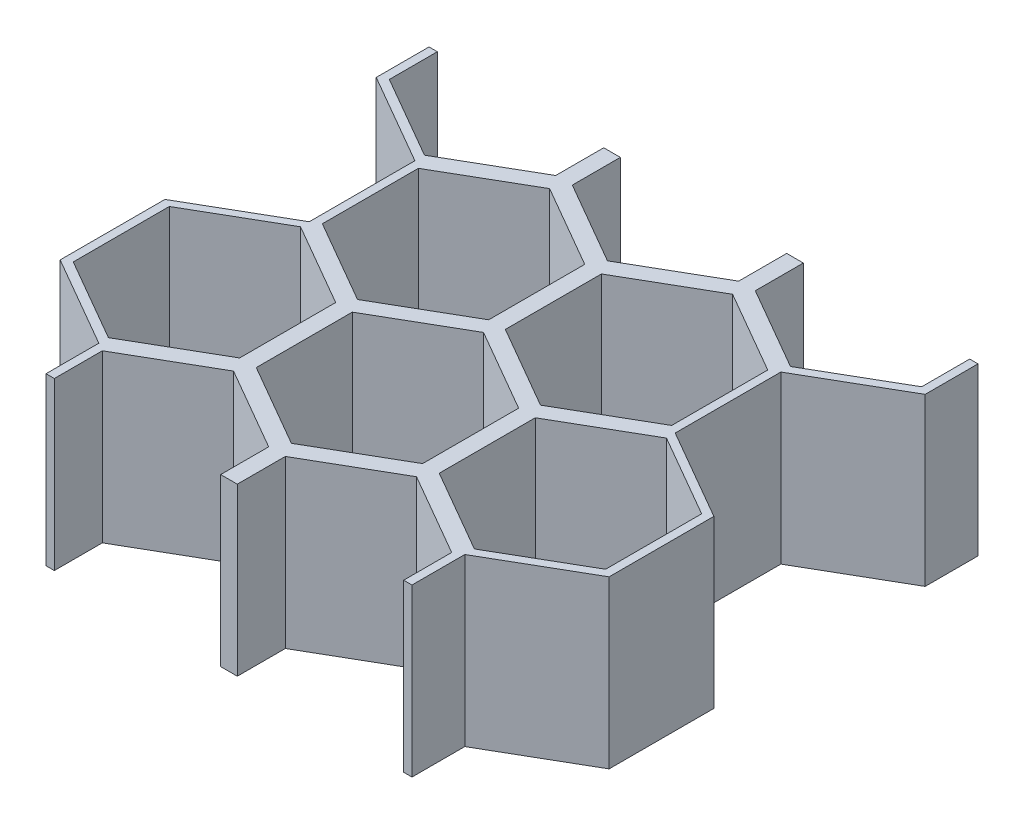
SolidWorks part; units mm, degrees
ref_plane "Front Plane" through (0, 0, 0) normal (0, 0, 1) x (1, 0, 0)
ref_plane "Top Plane" through (0, 0, 0) normal (0, 1, 0) x (1, 0, 0)
ref_plane "Right Plane" through (0, 0, 0) normal (1, 0, 0) x (0, 0, -1)
sketch "Sketch1" plane through (0, 0, 0) normal (0, 1, 0) x (1, 0, 0)
  line L0 (22, 11.547) -> (12, 5.7735)
  line L1 (0, 11.547) -> (-10, 5.7735)
  line L2 (-10, 5.7735) -> (-10, -5.7735)
  line L3 (-10, -5.7735) -> (0, -11.547)
  line L4 (0, -11.547) -> (10, -5.7735)
  line L5 (10, -5.7735) -> (10, 5.7735)
  line L6 (10, 5.7735) -> (0, 11.547)
  line L7 (11, -30.5996) -> (21, -24.8261)
  line L8 (21, -24.8261) -> (21, -13.2791)
  line L9 (21, -13.2791) -> (11, -7.5056)
  line L10 (11, -7.5056) -> (1, -13.2791)
  line L11 (1, -13.2791) -> (1, -24.8261)
  line L12 (1, -24.8261) -> (11, -30.5996)
  line L13 (12, 5.7735) -> (12, -5.7735)
  line L14 (12, -5.7735) -> (22, -11.547)
  line L15 (22, -11.547) -> (32, -5.7735)
  line L16 (32, -5.7735) -> (32, 5.7735)
  line L17 (32, 5.7735) -> (22, 11.547)
  line L18 (33, -30.5996) -> (43, -24.8261)
  line L19 (43, -24.8261) -> (43, -13.2791)
  line L20 (43, -13.2791) -> (33, -7.5056)
  line L21 (33, -7.5056) -> (23, -13.2791)
  line L22 (23, -13.2791) -> (23, -24.8261)
  line L23 (23, -24.8261) -> (33, -30.5996)
  line L24 (44, 11.547) -> (34, 5.7735)
  line L25 (34, 5.7735) -> (34, -5.7735)
  line L26 (34, -5.7735) -> (44, -11.547)
  line L27 (44, -11.547) -> (54, -5.7735)
  line L28 (54, -5.7735) -> (54, 5.7735)
  line L29 (54, 5.7735) -> (44, 11.547)
  line L30 (55, -30.5996) -> (65, -24.8261)
  line L31 (65, -24.8261) -> (65, -13.2791)
  line L32 (65, -13.2791) -> (55, -7.5056)
  line L33 (55, -7.5056) -> (45, -13.2791)
  line L34 (45, -13.2791) -> (45, -24.8261)
  line L35 (45, -24.8261) -> (55, -30.5996)
  line L36 (22, 49.547) -> (12, 43.7735)
  line L37 (12, 43.7735) -> (12, 32.2265)
  line L38 (12, 32.2265) -> (22, 26.453)
  line L39 (22, 26.453) -> (32, 32.2265)
  line L40 (32, 32.2265) -> (32, 43.7735)
  line L41 (32, 43.7735) -> (22, 49.547)
  line L42 (33, 7.4004) -> (43, 13.1739)
  line L43 (43, 13.1739) -> (43, 24.7209)
  line L44 (43, 24.7209) -> (33, 30.4944)
  line L45 (33, 30.4944) -> (23, 24.7209)
  line L46 (23, 24.7209) -> (23, 13.1739)
  line L47 (23, 13.1739) -> (33, 7.4004)
  line L48 (44, 49.547) -> (34, 43.7735)
  line L49 (34, 43.7735) -> (34, 32.2265)
  line L50 (34, 32.2265) -> (44, 26.453)
  line L51 (44, 26.453) -> (54, 32.2265)
  line L52 (54, 32.2265) -> (54, 43.7735)
  line L53 (54, 43.7735) -> (44, 49.547)
  line L54 (55, 7.4004) -> (65, 13.1739)
  line L55 (65, 13.1739) -> (65, 24.7209)
  line L56 (65, 24.7209) -> (55, 30.4944)
  line L57 (55, 30.4944) -> (45, 24.7209)
  line L58 (45, 24.7209) -> (45, 13.1739)
  line L59 (45, 13.1739) -> (55, 7.4004)
  line L60 (0, 49.547) -> (-10, 43.7735)
  line L61 (-10, 43.7735) -> (-10, 32.2265)
  line L62 (-10, 32.2265) -> (0, 26.453)
  line L63 (0, 26.453) -> (10, 32.2265)
  line L64 (10, 32.2265) -> (10, 43.7735)
  line L65 (10, 43.7735) -> (0, 49.547)
  line L66 (11, 7.4004) -> (21, 13.1739)
  line L67 (21, 13.1739) -> (21, 24.7209)
  line L68 (21, 24.7209) -> (11, 30.4944)
  line L69 (11, 30.4944) -> (1, 24.7209)
  line L70 (1, 24.7209) -> (1, 13.1739)
  line L71 (1, 13.1739) -> (11, 7.4004)
  line L72 (66, 11.547) -> (56, 5.7735)
  line L74 (11, -19.0526) -> (11, 38)
  line L75 (11, 38) -> (66, 38)
  line L77 (56, 5.7735) -> (56, -5.7735)
  line L78 (56, -5.7735) -> (66, -11.547)
  line L79 (66, -11.547) -> (76, -5.7735)
  line L80 (76, -5.7735) -> (76, 5.7735)
  line L81 (76, 5.7735) -> (66, 11.547)
  line L82 (77, -30.5996) -> (87, -24.8261)
  line L83 (87, -24.8261) -> (87, -13.2791)
  line L84 (87, -13.2791) -> (77, -7.5056)
  line L85 (77, -7.5056) -> (67, -13.2791)
  line L86 (67, -13.2791) -> (67, -24.8261)
  line L87 (67, -24.8261) -> (77, -30.5996)
  line L88 (66, 49.547) -> (56, 43.7735)
  line L89 (56, 43.7735) -> (56, 32.2265)
  line L90 (56, 32.2265) -> (66, 26.453)
  line L91 (66, 26.453) -> (76, 32.2265)
  line L92 (76, 32.2265) -> (76, 43.7735)
  line L93 (76, 43.7735) -> (66, 49.547)
  line L94 (77, 7.4004) -> (87, 13.1739)
  line L95 (87, 13.1739) -> (87, 24.7209)
  line L96 (87, 24.7209) -> (77, 30.4944)
  line L97 (77, 30.4944) -> (67, 24.7209)
  line L98 (67, 24.7209) -> (67, 13.1739)
  line L99 (67, 13.1739) -> (77, 7.4004)
  line L100 (11, -19.0526) -> (77, -19.0526)
  line L101 (77, -19.0526) -> (77, 38)
  line L102 (77, 38) -> (66, 38)
  circle A0 centre (0, 0) radius 10 construction
  circle A1 centre (11, -19.0526) radius 10 construction
  circle A2 centre (22, 0) radius 10 construction
  circle A3 centre (33, -19.0526) radius 10 construction
  circle A4 centre (44, 0) radius 10 construction
  circle A5 centre (55, -19.0526) radius 10 construction
  circle A6 centre (22, 38) radius 10 construction
  circle A7 centre (33, 18.9474) radius 10 construction
  circle A8 centre (44, 38) radius 10 construction
  circle A9 centre (55, 18.9474) radius 10 construction
  circle A10 centre (0, 38) radius 10 construction
  circle A11 centre (11, 18.9474) radius 10 construction
  circle A12 centre (66, 0) radius 10 construction
  circle A13 centre (77, -19.0526) radius 10 construction
  circle A14 centre (66, 38) radius 10 construction
  circle A15 centre (77, 18.9474) radius 10 construction
  dimension "D1" = 20
  dimension "D2" = 2
  dimension "D3" = 1
  dimension "D4" = 4
  dimension "D5" = 2
extrude "Boss-Extrude2" add sketch "Sketch1" along normal blind 20
sketch "Sketch2" plane through (0, 20, 0) normal (0, 1, 0) x (1, 0, 0)
  line L0 (11, 6.2457) -> (22, 12.5966)
  line L1 (11, -7.5056) -> (11, 7.4004) construction
  line L2 (22, 12.5966) -> (22, 25.2983)
  line L3 (22, 25.2983) -> (11, 31.6491)
  line L4 (11, 30.4944) -> (11, 38) construction
  line L5 (11, -6.3509) -> (22, -12.7017)
  line L6 (22, -12.7017) -> (22, -19.0526)
  line L9 (21, -13.2791) -> (11, -7.5056) construction
  line L11 (11, 7.4004) -> (21, 13.1739) construction
  line L13 (21, 24.7209) -> (11, 30.4944) construction
  line L14 (11, 6.2457) -> (11, -6.3509)
  line L15 (11, 31.6491) -> (2.2959, -19.0526)
  line L16 (2.2959, -19.0526) -> (22, -19.0526)
  line L17 (21, -19.0526) -> (23, -19.0526) construction
  line L19 (44, 26.453) -> (44, -11.547) construction
  line L20 (77, 31.6491) -> (85.7041, -19.0526)
  line L21 (66, 25.2983) -> (77, 31.6491)
  line L22 (66, 12.5966) -> (66, 25.2983)
  line L23 (77, 6.2457) -> (66, 12.5966)
  line L24 (77, 6.2457) -> (77, -6.3509)
  line L25 (77, -6.3509) -> (66, -12.7017)
  line L26 (66, -12.7017) -> (66, -19.0526)
  line L27 (85.7041, -19.0526) -> (66, -19.0526)
  point P18 (22, -19.0526)
  dimension "D1" = 1
  dimension "D2" = 1
  dimension "D3" = 1
extrude "Cut-Extrude1" cut sketch "Sketch2" against normal through all
equation "\"parois_t\"= 2mm"
equation "\"panneau_t\" = 20mm"
equation "\"entreplat_interne\"= 20mm"
equation "\"D1@Sketch1\"=\"entreplat_interne\""
equation "\"D2@Sketch1\"=\"parois_t\""
